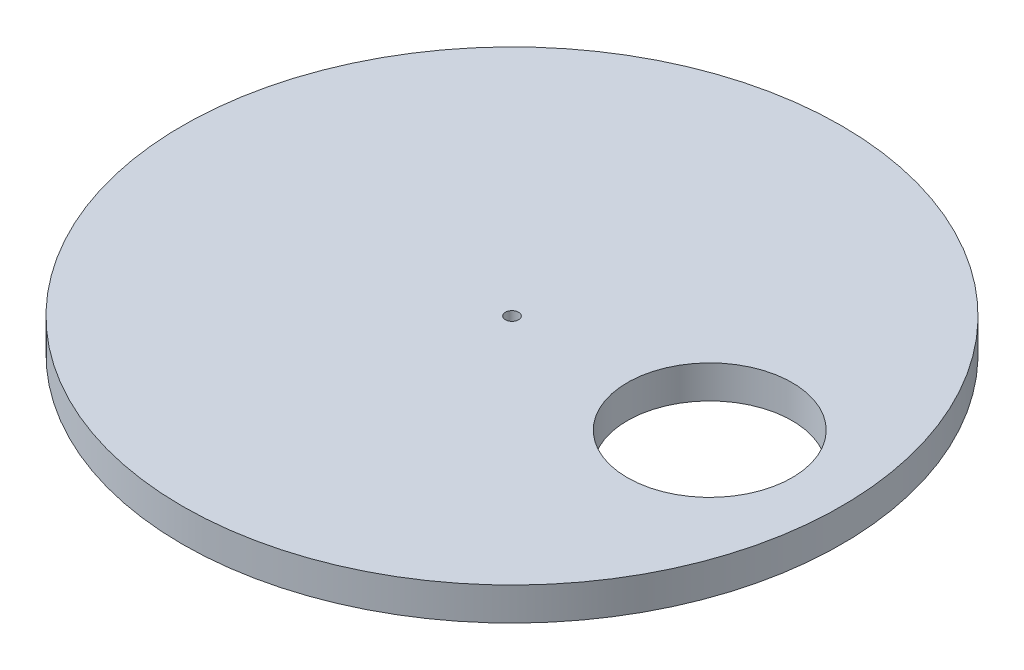
SolidWorks part; units mm, degrees
ref_plane "Alzado" through (0, 0, 0) normal (0, 0, 1) x (1, 0, 0)
ref_plane "Planta" through (0, 0, 0) normal (0, 1, 0) x (1, 0, 0)
ref_plane "Vista lateral" through (0, 0, 0) normal (1, 0, 0) x (0, 0, -1)
sketch "Croquis1" plane through (0, 0, 0) normal (0, 1, 0) x (1, 0, 0)
  line L0 (0, 11.8707) -> (0, -11.098) construction
  line L1 (-12.2219, 0) -> (13.7671, 0) construction
  circle A0 centre (0, 0) radius 100
  circle A1 centre (60, 0) radius 25
  circle A2 centre (0, 0) radius 2
  dimension "D1" = 200
  dimension "D2" = 50
  dimension "D4" = 4
  dimension "D3" = 60
extrude "Saliente-Extruir1" add sketch "Croquis1" along normal blind 10
